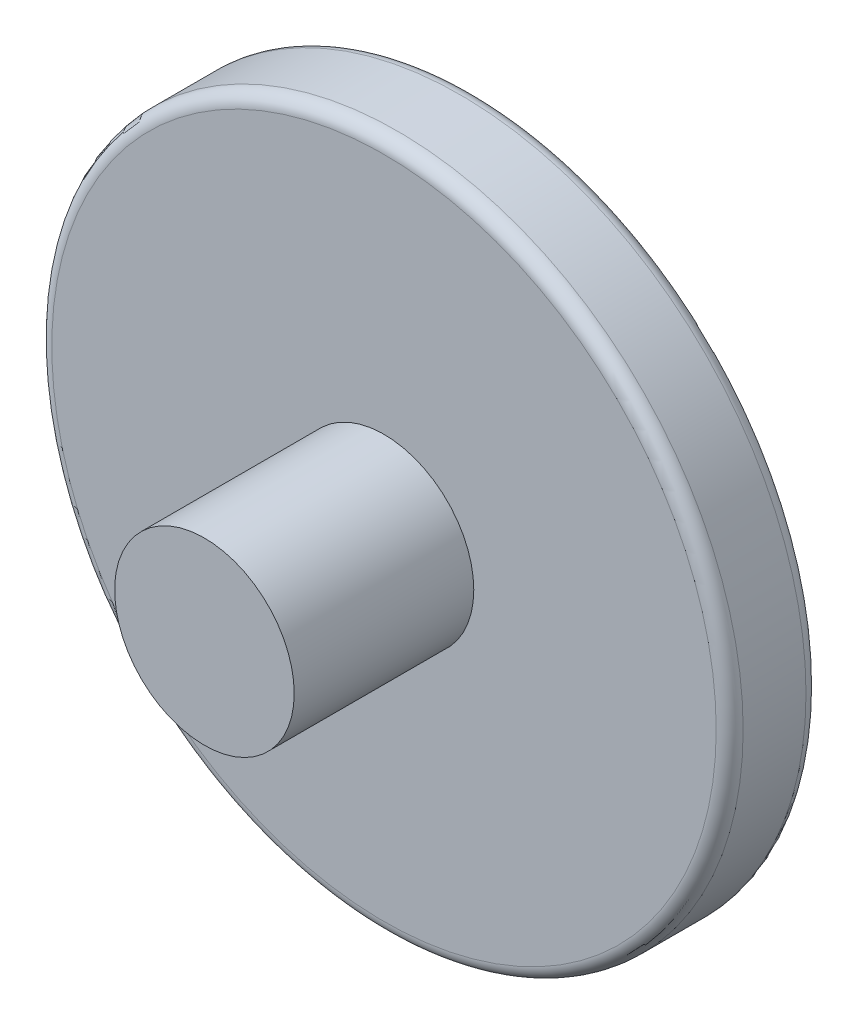
SolidWorks part; units mm, degrees
ref_plane "Front Plane" through (0, 0, 0) normal (0, 0, 1) x (1, 0, 0)
ref_plane "Top Plane" through (0, 0, 0) normal (0, 1, 0) x (1, 0, 0)
ref_plane "Right Plane" through (0, 0, 0) normal (1, 0, 0) x (0, 0, -1)
sketch "Sketch1" plane through (0, 0, 0) normal (0, 0, 1) x (1, 0, 0)
  circle A0 centre (0, 0) radius 7.7
extrude "Extrude1" add sketch "Sketch1" along normal blind 2
fillet "Fillet1" radius 0.3 2 edges at (7.7, 0, 2) (7.7, 0, 0)
sketch "Sketch2" plane through (0, 0, 0) normal (0, 0, -1) x (-1, 0, 0)
  line L1 (3.0496, 0) -> (1.5248, 2.641)
  line L2 (1.5248, 2.641) -> (-1.5248, 2.641)
  line L3 (-1.5248, 2.641) -> (-3.0496, 0)
  line L4 (-3.0496, 0) -> (-1.5248, -2.641)
  line L5 (-1.5248, -2.641) -> (1.5248, -2.641)
  line L6 (1.5248, -2.641) -> (3.0496, 0)
  circle A0 centre (0, 0) radius 2.641 construction
extrude "Extrude2" cut sketch "Sketch2" against normal blind 1.5
fillet "Fillet2" radius 0.3 18 edges at (-2.2872, 1.3205, 0) (-3.0496, 0, 0.75) (-2.2872, -1.3205, 0) (-1.5248, -2.641, 0.75) (0, -2.641, 0) (1.5248, -2.641, 0.75) (2.2872, -1.3205, 0) (3.0496, 0, 0.75) (2.2872, 1.3205, 0) (-1.5248, 2.641, 0.75) (1.5248, 2.641, 0.75) (0, 2.641, 0) (0, -2.641, 1.5) (2.2872, -1.3205, 1.5) (2.2872, 1.3205, 1.5) (0, 2.641, 1.5) (-2.2872, 1.3205, 1.5) (-2.2872, -1.3205, 1.5)
sketch "Sketch3" plane through (0, 0, 2) normal (0, 0, 1) x (1, 0, 0)
  circle A0 centre (0, 0) radius 2
extrude "Extrude4" add sketch "Sketch3" along normal blind 4
